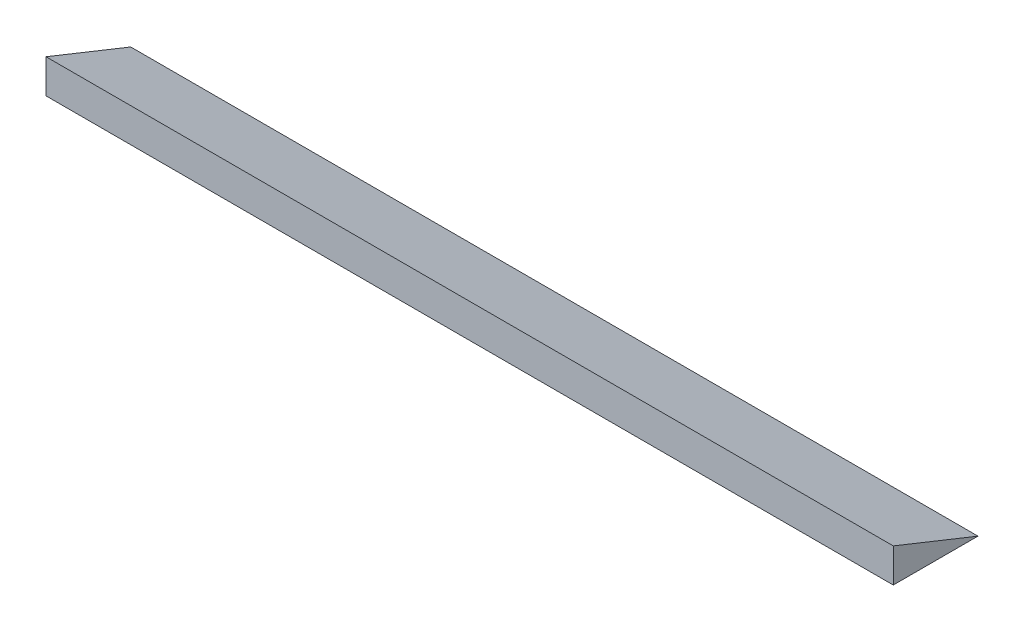
SolidWorks part; units mm, degrees
ref_plane "Front Plane" through (0, 0, 0) normal (0, 0, 1) x (1, 0, 0)
ref_plane "Top Plane" through (0, 0, 0) normal (0, 1, 0) x (1, 0, 0)
ref_plane "Right Plane" through (0, 0, 0) normal (1, 0, 0) x (0, 0, -1)
sketch "Sketch1" plane through (0, 0, 0) normal (1, 0, 0) x (0, 0, -1)
  line L0 (0, 0) -> (100, 0)
  line L1 (100, 0) -> (0, 40)
  line L2 (0, 40) -> (0, 0)
  dimension "D1" = 100
  dimension "D2" = 40
extrude "Boss-Extrude1" add sketch "Sketch1" along normal blind 1000
